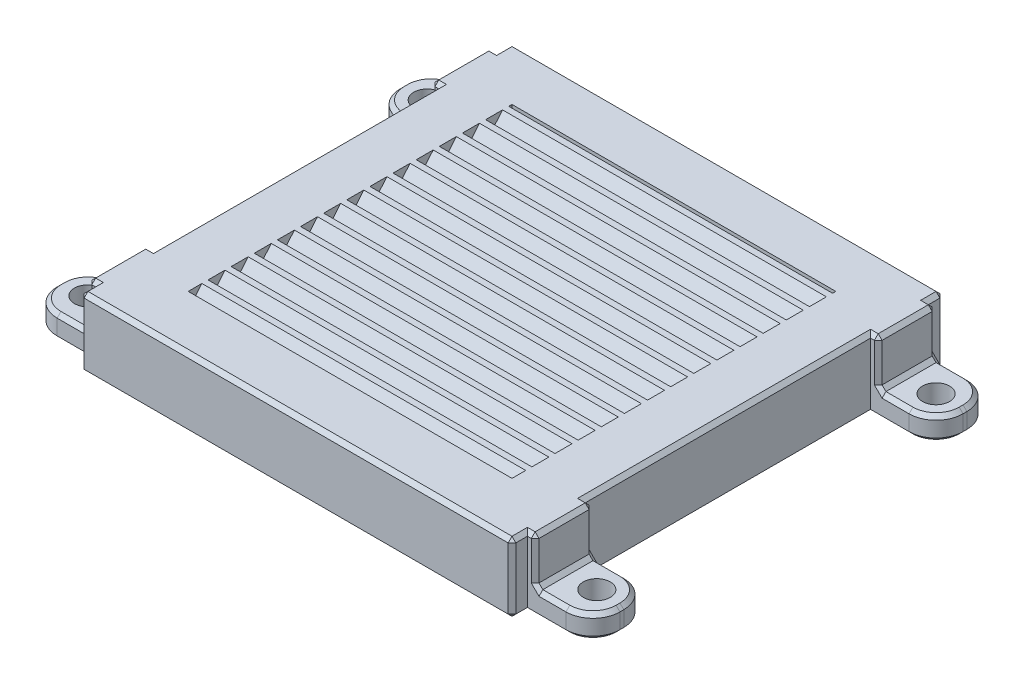
SolidWorks part; units mm, degrees
ref_plane "Alzado" through (0, 0, 0) normal (0, 0, 1) x (1, 0, 0)
ref_plane "Planta" through (0, 0, 0) normal (0, 1, 0) x (1, 0, 0)
ref_plane "Vista lateral" through (0, 0, 0) normal (1, 0, 0) x (0, 0, -1)
sketch "Croquis1" plane through (0, 0, 0) normal (0, 1, 0) x (1, 0, 0)
  line L1 (-26, -26) -> (26, -26)
  line L2 (-26, -26) -> (-26, 26)
  line L3 (-26, 26) -> (26, 26)
  line L4 (26, -26) -> (26, 26)
  line L5 (-26, -26) -> (26, 26) construction
  line L6 (-26, 26) -> (26, -26) construction
  line L7 (-21, -21) -> (21, -21)
  line L8 (-21, -21) -> (-21, 21)
  line L9 (-21, 21) -> (21, 21)
  line L10 (21, -21) -> (21, 21)
  line L11 (-21, -21) -> (21, 21) construction
  line L12 (-21, 21) -> (21, -21) construction
  point P0 (0, 0)
  point P6 (0, 0)
  dimension "D1" = 52
  dimension "D2" = 52
  dimension "D3" = 5
extrude "Saliente-Extruir1" add sketch "Croquis1" along normal blind 2
sketch "Croquis8" plane through (-21, 0, 0) normal (1, 0, 0) x (0, 0, -1)
  line L0 (-20.9, 0) -> (-19.2218, 2)
  line L1 (21, 0) -> (-21, 0) construction
  line L2 (21, 2) -> (-21, 2) construction
  line L3 (-19.2218, 2) -> (-18.4218, 2)
  line L4 (-18.4218, 2) -> (-20.1, 0)
  line L5 (-20.1, 0) -> (-20.9, 0)
  line L6 (-17.1, 0) -> (-17.9, 0)
  line L87 (-21, 2) -> (-21, 0) construction
  line L88 (-17.9, 0) -> (-16.2218, 2)
  line L89 (-16.2218, 2) -> (-15.4218, 2)
  line L90 (-15.4218, 2) -> (-17.1, 0)
  line L91 (-14.1, 0) -> (-14.9, 0)
  line L92 (-14.9, 0) -> (-13.2218, 2)
  line L93 (-13.2218, 2) -> (-12.4218, 2)
  line L94 (-12.4218, 2) -> (-14.1, 0)
  line L95 (-11.1, 0) -> (-11.9, 0)
  line L96 (-11.9, 0) -> (-10.2218, 2)
  line L97 (-10.2218, 2) -> (-9.4218, 2)
  line L98 (-9.4218, 2) -> (-11.1, 0)
  line L99 (-8.1, 0) -> (-8.9, 0)
  line L100 (-8.9, 0) -> (-7.2218, 2)
  line L101 (-7.2218, 2) -> (-6.4218, 2)
  line L102 (-6.4218, 2) -> (-8.1, 0)
  line L103 (-5.1, 0) -> (-5.9, 0)
  line L104 (-5.9, 0) -> (-4.2218, 2)
  line L105 (-4.2218, 2) -> (-3.4218, 2)
  line L106 (-3.4218, 2) -> (-5.1, 0)
  line L107 (-2.1, 0) -> (-2.9, 0)
  line L108 (-2.9, 0) -> (-1.2218, 2)
  line L109 (-1.2218, 2) -> (-0.4218, 2)
  line L110 (-0.4218, 2) -> (-2.1, 0)
  line L111 (0.9, 0) -> (0.1, 0)
  line L112 (0.1, 0) -> (1.7782, 2)
  line L113 (1.7782, 2) -> (2.5782, 2)
  line L114 (2.5782, 2) -> (0.9, 0)
  line L115 (3.9, 0) -> (3.1, 0)
  line L116 (3.1, 0) -> (4.7782, 2)
  line L117 (4.7782, 2) -> (5.5782, 2)
  line L118 (5.5782, 2) -> (3.9, 0)
  line L119 (6.9, 0) -> (6.1, 0)
  line L120 (6.1, 0) -> (7.7782, 2)
  line L121 (7.7782, 2) -> (8.5782, 2)
  line L122 (8.5782, 2) -> (6.9, 0)
  line L123 (9.9, 0) -> (9.1, 0)
  line L124 (9.1, 0) -> (10.7782, 2)
  line L125 (10.7782, 2) -> (11.5782, 2)
  line L126 (11.5782, 2) -> (9.9, 0)
  line L127 (12.9, 0) -> (12.1, 0)
  line L128 (12.1, 0) -> (13.7782, 2)
  line L129 (13.7782, 2) -> (14.5782, 2)
  line L130 (14.5782, 2) -> (12.9, 0)
  line L131 (15.9, 0) -> (15.1, 0)
  line L132 (15.1, 0) -> (16.7782, 2)
  line L133 (16.7782, 2) -> (17.5782, 2)
  line L134 (17.5782, 2) -> (15.9, 0)
  line L135 (18.9, 0) -> (18.1, 0)
  line L136 (18.1, 0) -> (19.7782, 2)
  line L137 (19.7782, 2) -> (20.5782, 2)
  line L138 (20.5782, 2) -> (18.9, 0)
  dimension "D1" = 0.8
  dimension "D2" = 0.1
  dimension "D3" = 50
extrude "Saliente-Extruir6" add sketch "Croquis8" along normal up to surface (42 mm away) up to face at (21, 1, 0)
sketch "Croquis4" plane through (26, 0, 0) normal (1, 0, 0) x (0, 0, -1)
  line L0 (-26, 2) -> (26, 2) construction
  line L1 (-26, 0) -> (-18.5, 0)
  line L2 (-26, 0) -> (-26, 2)
  line L3 (-26, 2) -> (-18.5, 2)
  line L4 (-18.5, 0) -> (-18.5, 2)
  line L5 (-26, 0) -> (26, 0) construction
  line L6 (26, 2) -> (18.5, 2)
  line L7 (26, 2) -> (26, 0)
  line L8 (26, 0) -> (18.5, 0)
  line L9 (18.5, 2) -> (18.5, 0)
  dimension "D1" = 7.5
  dimension "D2" = 7.5
extrude "Saliente-Extruir3" add sketch "Croquis4" along normal blind 3
sketch "Croquis5" plane through (0, 0, 0) normal (0, -1, 0) x (1, 0, 0)
  line L0 (29, 18.5) -> (26, 18.5) construction
  line L1 (29, 26) -> (26, 26)
  line L2 (29, 26) -> (29, 18.5)
  line L3 (29, 18.5) -> (26, 18.5)
  line L4 (26, 26) -> (26, 18.5)
  line L5 (29, -26) -> (-26, -26) construction
  line L6 (29, -18.5) -> (26, -18.5)
  line L7 (29, -18.5) -> (29, -26)
  line L8 (29, -26) -> (26, -26)
  line L9 (26, -18.5) -> (26, -26)
  dimension "D1" = 3
  dimension "D2" = 3
extrude "Saliente-Extruir4" add sketch "Croquis5" along normal blind 7
sketch "Croquis6" plane through (29, 0, 0) normal (1, 0, 0) x (0, 0, -1)
  line L0 (-18.5, -7) -> (-18.5, 2) construction
  line L1 (-26, -7) -> (-18.5, -7)
  line L2 (-26, -7) -> (-26, -4)
  line L3 (-26, -4) -> (-18.5, -4)
  line L4 (-18.5, -7) -> (-18.5, -4)
  line L5 (26, -7) -> (26, 2) construction
  line L6 (18.5, -7) -> (26, -7)
  line L7 (18.5, -7) -> (18.5, -4)
  line L8 (18.5, -4) -> (26, -4)
  line L9 (26, -7) -> (26, -4)
  dimension "D1" = 3
extrude "Saliente-Extruir5" add sketch "Croquis6" along normal blind 7.5
sketch "Croquis7" plane through (0, -4, 0) normal (0, 1, 0) x (1, 0, 0)
  line L0 (36.5, 26) -> (36.5, 18.5) construction
  line L1 (36.5, 26) -> (29, 26) construction
  line L2 (36.5, -18.5) -> (36.5, -26) construction
  line L4 (36.5, -26) -> (29, -26) construction
  circle A0 centre (33, -22) radius 1.75
  circle A1 centre (33, 22) radius 1.75
  dimension "D1" = 3.5
  dimension "D2" = 3.5
  dimension "D6" = 4
  dimension "D3" = 3.5
  dimension "D4" = 4
  dimension "D5" = 3.5
extrude "Cortar-Extruir1" cut sketch "Croquis7" against normal blind 7.5
mirror "Simetría1" about plane through (0, 0, 0) normal (1, 0, 0) of "Cortar-Extruir1", "Saliente-Extruir4", "Saliente-Extruir5", "Saliente-Extruir3"
sketch "Croquis9" plane through (0, 2, 0) normal (0, 1, 0) x (1, 0, 0)
  line L1 (-28, 28) -> (28, 28)
  line L2 (-28, 28) -> (-28, -28)
  line L3 (-28, -28) -> (28, -28)
  line L4 (28, 28) -> (28, -28)
  line L5 (-26, 26) -> (26, 26)
  line L6 (-26, 26) -> (-26, -26)
  line L7 (-26, -26) -> (26, -26)
  line L8 (26, 26) -> (26, -26)
  dimension "D1" = 2
  dimension "D2" = 2
  dimension "D3" = 2
  dimension "D4" = 2
extrude "Saliente-Extruir7" add sketch "Croquis9" against normal up to surface (9 mm away)
fillet "Redondeo1" radius 3.5 8 edges at (36.5, -5.5, 26) (36.5, -5.5, 18.5) (36.5, -5.5, -18.5) (36.5, -5.5, -26) (-36.5, -5.5, 26) (-36.5, -5.5, 18.5) (-36.5, -5.5, -18.5) (-36.5, -5.5, -26)
chamfer "Chaflán1" distance 0.5 angle 45 91 edges at (-28.5, 2, 26) (28.5, 2, 18.5) (29, -1, 26) (29, 2, 22.25) (28.5, 2, -18.5) (29, 2, -22.25) (29, -1, -18.5) (26, -7, 0) (29, -1, 18.5) (29, -4, 22.25) (29, -1, -26) (29, -4, -22.25) (33, -7, 23.75) (33, -7, -20.25) (-29, -1, 26) (-29, 2, 22.25) (-28.5, 2, 18.5) (-29, -1, -18.5) (-29, 2, -22.25) (-28.5, 2, -18.5) (-26, -7, 0) (-29, -1, 18.5) (-29, -4, 22.25) (-29, -1, -26) (-29, -4, -22.25) (-33, -7, 23.75) (-33, -7, -20.25) (-30.5, -7, -26) (-30.5, -7, 18.5) (30.5, -7, -26) (30.5, -7, 18.5) (28.5, 2, 26) (-28.5, 2, -26) (28, -2.5, -28) (28, 2, -27) (0, 2, -28) (-28, 2, -27) (-28, 2, 27) (0, 2, 28) (28, 2, 27) (28, 2, 0) (28, -7, -27) (-28, -7, -27) (0, -7, -28) (-28, -7, 27) (28, -7, 27) (0, -7, 28) (28, -7, 0) (-28, -2.5, 28) (28, -2.5, 28) (-28, 2, 0) (0, -7, 26) (0, -7, -26) (-28, -7, 0) (36.5, -7, -22.25) (36.5, -4, -22.25) (31, -4, -18.5) (31, -4, -26) (35.4749, -4, -19.5251) (35.4749, -4, -24.9749) (30.5, -7, -18.5) (36.5, -7, 22.25) (30.5, -7, 26) (-30.5, -7, 26) (-36.5, -7, 22.25) (-30.5, -7, -18.5) (-36.5, -7, -22.25) (-35.4749, -7, 24.9749) (-35.4749, -7, 19.5251) (-35.4749, -7, -24.9749) (-35.4749, -7, -19.5251) (35.4749, -7, 24.9749) (35.4749, -7, 19.5251) (35.4749, -7, -19.5251) (35.4749, -7, -24.9749) (36.5, -4, 22.25) (31, -4, 26) (31, -4, 18.5) (35.4749, -4, 24.9749) (35.4749, -4, 19.5251) (-31, -4, -18.5) (-36.5, -4, -22.25) (-31, -4, -26) (-35.4749, -4, -24.9749) (-35.4749, -4, -19.5251) (-31, -4, 18.5) (-36.5, -4, 22.25) (-31, -4, 26) (-35.4749, -4, 24.9749) (-35.4749, -4, 19.5251) (28.5, 2, -26)
